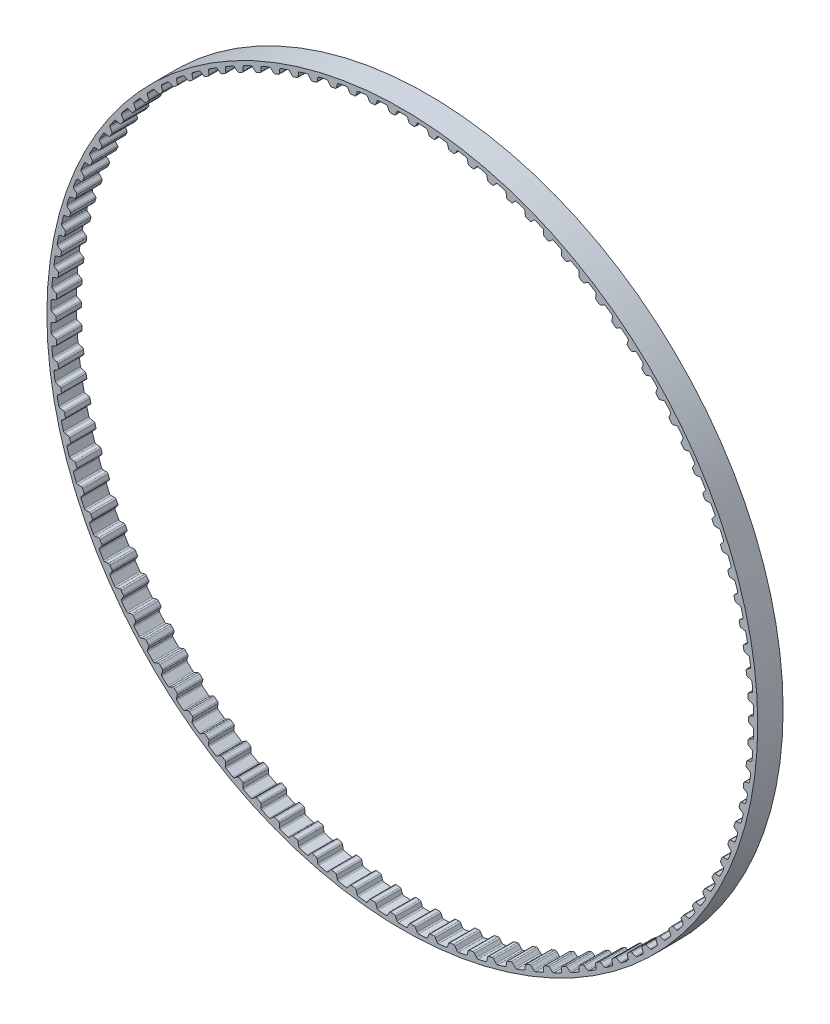
SolidWorks part; units mm, degrees
ref_plane "Front Plane" through (0, 0, 0) normal (0, 0, 1) x (1, 0, 0)
ref_plane "Top Plane" through (0, 0, 0) normal (0, 1, 0) x (1, 0, 0)
ref_plane "Right Plane" through (0, 0, 0) normal (1, 0, 0) x (0, 0, -1)
sketch "Sketch1" plane through (0, 0, 0) normal (0, 0, 1) x (1, 0, 0)
  line L0 (0, 0) -> (-2.4744, 86.6145) construction
  line L1 (0, 0) -> (2.4744, 86.6145) construction
  line L2 (2.4744, 86.6145) -> (-2.4744, 86.6145) construction
  line L3 (2.4744, 86.6145) -> (-2.4744, 86.6145) construction
  circle A0 centre (0, 0) radius 88.9359
  circle A1 centre (0, 0) radius 86.6499
  circle A2 centre (0, 0) radius 87.9199 construction
  dimension "OD" = 177.8717
  dimension "Angle Distance" = 3.273
  dimension "hs" = 2.286
  dimension "ht" = 1.27
extrude "Boss-Extrude1" add sketch "Sketch1" along normal mid plane 6.35
sketch "Sketch2" plane through (0, 0, 0) normal (0, 0, 1) x (1, 0, 0)
  line L1 (0, 88.9359) -> (0, 0) construction
  line L2 (-2.54, 87.2728) -> (2.54, 87.2728) construction
  line L4 (-1.7793, 86.6344) -> (-3.1695, 86.5947)
  line L5 (-1.7793, 86.6344) -> (-1.2277, 87.9113)
  line L6 (-3.1695, 86.5947) -> (-3.7931, 87.838)
  line L7 (0, 0) -> (-2.4744, 86.6145) construction
  line L8 (-1.2277, 87.9113) -> (-3.7931, 87.838) construction
  line L9 (1.2277, 87.9113) -> (3.7931, 87.838) construction
  line L10 (3.1695, 86.5947) -> (3.7931, 87.838)
  line L11 (1.7793, 86.6344) -> (1.2277, 87.9113)
  line L12 (1.7793, 86.6344) -> (3.1695, 86.5947)
  line L13 (0, 0) -> (34.0343, 82.166) construction
  line L14 (-2.54, 87.2728) -> (-7.6114, 86.9774) construction
  line L15 (-5.0757, 87.1251) -> (0, 0) construction
  line L16 (-7.6114, 86.9774) -> (-7.5539, 86.32) construction
  circle A0 centre (0, 0) radius 87.9199 construction
  circle A1 centre (0, 0) radius 87.9199
  circle A2 centre (0, 0) radius 87.2728 construction
  circle A4 centre (0, 0) radius 88.9359 construction
  circle A5 centre (0, 0) radius 86.6499 construction
  point P16 (-1.5035, 87.2728)
  point P20 (0, 87.2728)
  point P29 (0, 0)
  dimension "D1" = 22.5
  dimension "bt" = 2.5654
  dimension "b" = 50
  dimension "Pitch" = 5.08
sketch "Sketch3" plane through (0, 0, 0) normal (0, 0, 1) x (1, 0, 0)
  line L0 (-2.0244, 86.6262) -> (2.0244, 86.6262)
  line L2 (-1.7793, 86.6344) -> (-1.2277, 87.9113) construction
  line L3 (1.7793, 86.6344) -> (1.2277, 87.9113) construction
  line L5 (-1.6835, 86.856) -> (-1.3256, 87.6845)
  line L7 (1.6835, 86.856) -> (1.3256, 87.6845)
  arc A0 (1.6835, 86.856) -> (2.0244, 86.6262) centre (2.0333, 87.0071) ccw
  circle A1 centre (0, 0) radius 87.9199 construction
  arc A2 (0.9801, 87.9144) -> (-0.9801, 87.9144) centre (0, 0) ccw
  arc A3 (-1.6835, 86.856) -> (-2.0244, 86.6262) centre (-2.0333, 87.0071) cw
  arc A4 (1.3256, 87.6845) -> (0.9801, 87.9144) centre (0.9759, 87.5334) ccw
  arc A5 (-1.3256, 87.6845) -> (-0.9801, 87.9144) centre (-0.9759, 87.5334) cw
  circle A6 centre (0, 0) radius 86.6499 construction
  arc A7 (-2.0244, 86.6262) -> (2.0244, 86.6262) centre (0, 0) ccw construction
  dimension "ra" = 0.381
  dimension "rr" = 0.381
extrude "Cut-Extrude1" cut sketch "Sketch3" against normal mid plane 6.35
pattern_circular "CirPattern1" count 110 over 360 about axis through (0, 0, 0) along (0, 0, 1) of "Cut-Extrude1"
equation "\"D1@Cut-Extrude1\" = \"Width@Boss-Extrude1\""
